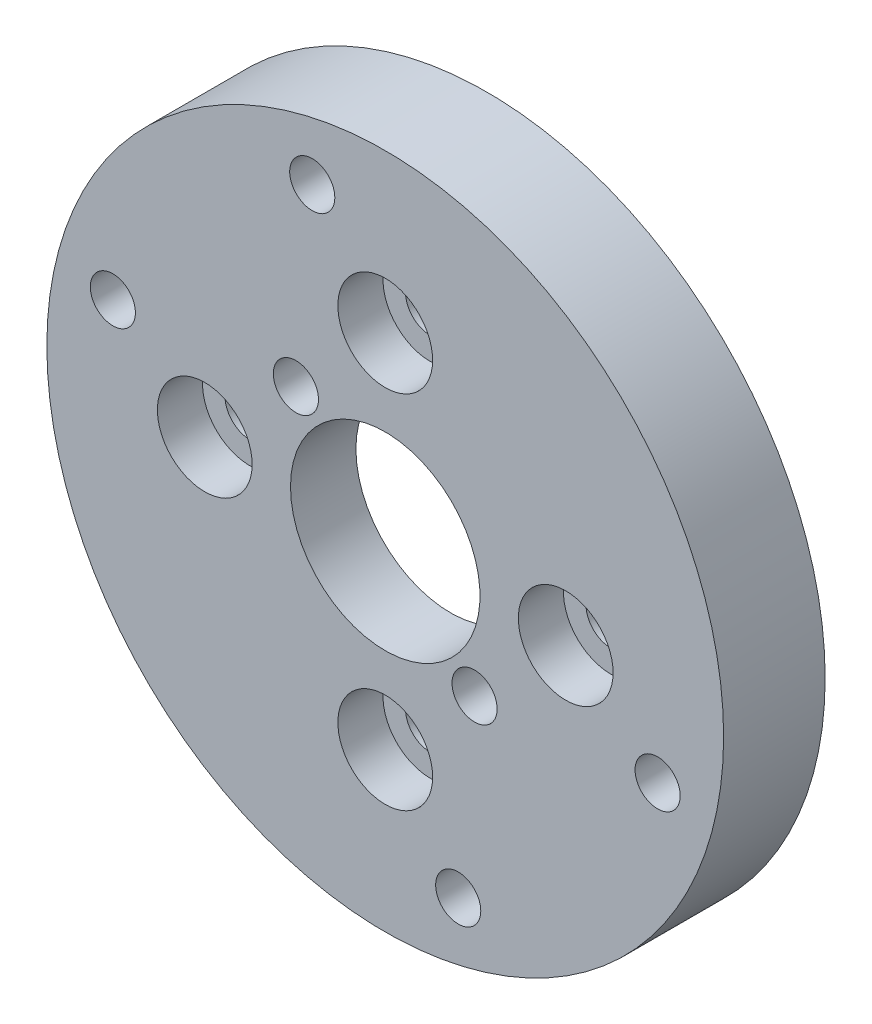
SolidWorks part; units mm, degrees
ref_plane "정면" through (0, 0, 0) normal (0, 0, 1) x (1, 0, 0)
ref_plane "윗면" through (0, 0, 0) normal (0, 1, 0) x (1, 0, 0)
ref_plane "우측면" through (0, 0, 0) normal (1, 0, 0) x (0, 0, -1)
sketch "스케치1" plane through (0, 0, 0) normal (0, 0, 1) x (1, 0, 0)
  line L0 (0, 0) -> (0, 15) construction
  line L1 (0, 0) -> (6.7175, 6.7175) construction
  line L2 (0, 0) -> (-3.2352, 12.0741) construction
  line L4 (0, 0) -> (-10.6066, 10.6066) construction
  circle A0 centre (0, 0) radius 2.3
  circle A1 centre (0, 0) radius 8 construction
  circle A2 centre (0, 0) radius 15
  circle A3 centre (0, 8) radius 1.1
  circle A4 centre (8, 0) radius 1.1
  circle A5 centre (0, -8) radius 1.1
  circle A6 centre (-8, 0) radius 1.1
  circle A7 centre (0, 0) radius 9.5 construction
  circle A8 centre (-3.2352, 12.0741) radius 1
  circle A9 centre (0, 0) radius 15 construction
  circle A10 centre (12.0741, -3.2352) radius 1
  circle A11 centre (3.2352, -12.0741) radius 1
  circle A12 centre (-12.0741, 3.2352) radius 1
  point P17 (0, 0)
  point P25 (0, 0)
  point P28 (0, 0)
  dimension "D1" = 4.6
  dimension "D2" = 16
  dimension "D3" = 30
  dimension "D4" = 2.2
  dimension "D6" = 19
  dimension "D8" = 12.5
  dimension "D9" = 2
  dimension "D7" = 45
  dimension "D10" = 60
  dimension "D5" = 4
extrude "보스-돌출1" add sketch "스케치1" along normal blind 4.5
sketch "스케치2" plane through (0, 0, 4.5) normal (0, 0, 1) x (1, 0, 0)
  circle A0 centre (0, 8) radius 2.1
  circle A1 centre (8, 0) radius 2.1
  circle A2 centre (0, -8) radius 2.1
  circle A3 centre (-8, 0) radius 2.1
  point P12 (0, 0)
  dimension "D2" = 4.2
  dimension "D1" = 4
extrude "컷-돌출1" cut sketch "스케치2" against normal blind 2
sketch "스케치10" plane through (0, 0, 0) normal (0, 0, -1) x (-1, 0, 0)
  circle A0 centre (0, 0) radius 10
  dimension "D1" = 20
extrude "컷-돌출7" cut sketch "스케치10" against normal blind 1.6
sketch "스케치9" plane through (0, 0, 1.6) normal (0, 0, -1) x (-1, 0, 0)
  circle A0 centre (0, 0) radius 4.2
  dimension "D1" = 8.4
extrude "컷-돌출5" cut sketch "스케치9" against normal through all
sketch "스케치6" plane through (0, 0, 4.5) normal (0, 0, 1) x (1, 0, 0)
  line L0 (0, 0) -> (-3.9598, 3.9598) construction
  line L1 (0, 0) -> (3.9598, -3.9598) construction
  line L2 (0, 0) -> (4.415, 0) construction
  circle A0 centre (-3.9598, 3.9598) radius 1
  circle A1 centre (3.9598, -3.9598) radius 1
  dimension "D2" = 2
  dimension "D4" = 2
  dimension "D1" = 5.6
  dimension "D3" = 5.6
  dimension "D5" = 45
extrude "컷-돌출6" cut sketch "스케치6" against normal blind 2
